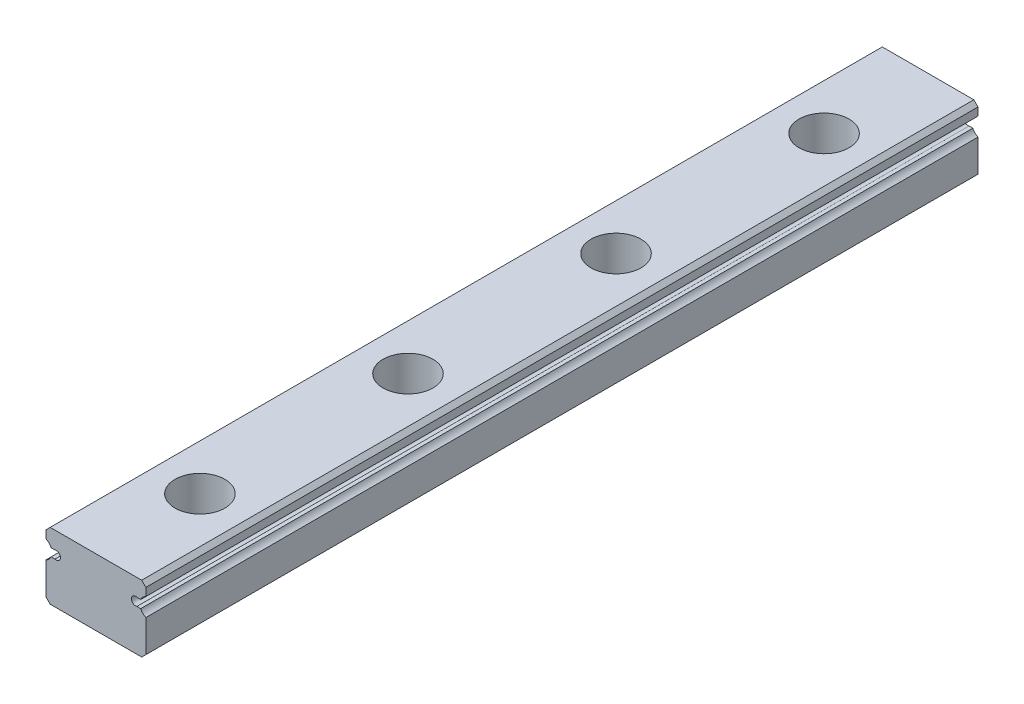
SolidWorks part; units mm, degrees
material "Chrome Stainless Steel"
ref_plane "Front Plane" through (0, 0, 0) normal (0, 0, 1) x (1, 0, 0)
ref_plane "Top Plane" through (0, 0, 0) normal (0, 1, 0) x (1, 0, 0)
ref_plane "Right Plane" through (0, 0, 0) normal (1, 0, 0) x (0, 0, -1)
sketch "Sketch1" plane through (0, 0, 0) normal (0, 0, 1) x (1, 0, 0)
  line L0 (0, 4) -> (0, -4) construction
  line L1 (5.5, -4) -> (-5.5, -4)
  line L2 (-5.5, -4) -> (-6, -3.5)
  line L3 (-6, -3.5) -> (-6, 0.3689)
  line L4 (5.5, 4) -> (-5.5, 4)
  line L5 (-5.5, 4) -> (-6, 3.5)
  line L6 (-6, 2.5511) -> (-6, 3.5)
  line L7 (-5.3839, 0.985) -> (-4.9211, 0.985)
  line L8 (-5.3839, 1.935) -> (-4.9211, 1.935)
  line L9 (5.3839, 0.985) -> (4.9211, 0.985)
  line L10 (5.5, 4) -> (6, 3.5)
  line L11 (6, 2.5511) -> (6, 3.5)
  line L12 (5.3839, 1.935) -> (4.9211, 1.935)
  line L13 (6, -3.5) -> (6, 0.3689)
  line L14 (5.5, -4) -> (6, -3.5)
  circle A0 centre (-6.475, 1.46) radius 1.19 construction
  circle A1 centre (-4.765, 1.46) radius 0.5 construction
  arc A2 (-6, 0.3689) -> (-5.3839, 0.985) centre (-6.475, 1.46) ccw
  arc A3 (-5.3839, 1.935) -> (-6, 2.5511) centre (-6.475, 1.46) ccw
  arc A4 (-4.9211, 0.985) -> (-4.9211, 1.935) centre (-4.765, 1.46) ccw
  arc A5 (5.3839, 1.935) -> (6, 2.5511) centre (6.475, 1.46) cw
  arc A6 (4.9211, 0.985) -> (4.9211, 1.935) centre (4.765, 1.46) cw
  arc A7 (6, 0.3689) -> (5.3839, 0.985) centre (6.475, 1.46) cw
  point P4 (0, 0)
  dimension "D5" = 5.46
  dimension "D6" = 6.475
  dimension "D7" = 2.38
  dimension "D11" = 1
  dimension "D12" = 5.46
  dimension "D13" = 4.765
  dimension "D1" = 8
  dimension "D2" = 0.5
  dimension "D3" = 0.5
  dimension "D4" = 6
  dimension "D8" = 0.5
  dimension "D9" = 0.5
  dimension "D10" = 6
  dimension "D14" = 0.475
  dimension "D15" = 0.475
extrude "Boss-Extrude1" add sketch "Sketch1" along normal blind 100 contours L13 A7 L9 A6 L12 A5 L11 L10 L4 L5 L6 A3 L8 A4 L7 A2 L3 L2 L1 L14
sketch "Sketch2" plane through (0, 4, 0) normal (0, 1, 0) x (1, 0, 0)
  line L0 (5.5, 0) -> (-5.5, 0) construction
  circle A0 centre (0, -12.5) radius 3
  dimension "D1" = 12.5
extrude "Cut-Extrude1" cut sketch "Sketch2" against normal blind 4.5
sketch "Sketch3" plane through (0, -0.5, 0) normal (0, 1, 0) x (1, 0, 0)
  circle A0 centre (0, -12.5) radius 1.75
extrude "Cut-Extrude2" cut sketch "Sketch3" against normal through all
pattern_linear "LPattern1" count 4 spacing 25 along (0, 0, 1) of "Cut-Extrude1", "Cut-Extrude2"
